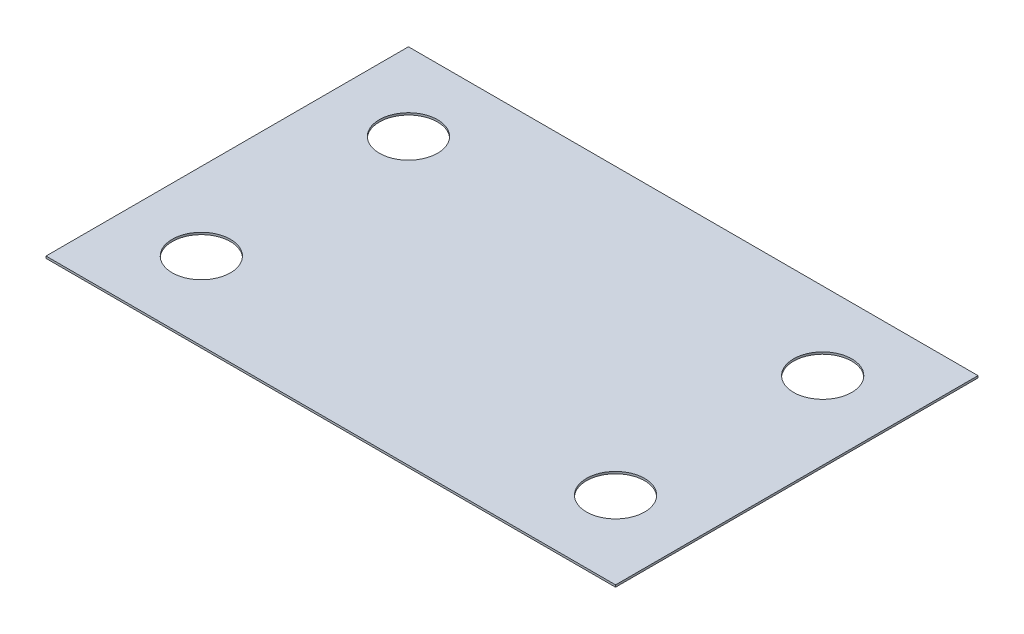
SolidWorks part; units mm, degrees
ref_plane "Front Plane" through (0, 0, 0) normal (0, 0, 1) x (1, 0, 0)
ref_plane "Top Plane" through (0, 0, 0) normal (0, 1, 0) x (1, 0, 0)
ref_plane "Right Plane" through (0, 0, 0) normal (1, 0, 0) x (0, 0, -1)
sketch "Sketch1" plane through (0, 0, 0) normal (0, 1, 0) x (1, 0, 0)
  line L0 (9.525, 9.525) -> (60.325, 9.525) construction
  line L1 (0, 0) -> (69.85, 0)
  line L2 (0, 0) -> (0, 44.45)
  line L3 (0, 44.45) -> (69.85, 44.45)
  line L4 (69.85, 0) -> (69.85, 44.45)
  line L5 (9.525, 9.525) -> (9.525, 34.925) construction
  circle A0 centre (34.925, 22.225) radius 1 construction
  circle A1 centre (9.525, 9.525) radius 3.5687
  circle A2 centre (9.525, 34.925) radius 3.5687
  circle A3 centre (60.325, 9.525) radius 3.5687
  circle A4 centre (60.325, 34.925) radius 3.5687
  point P8 (34.925, 44.45)
  point P10 (0, 22.225)
  point P17 (0, 0)
  point P18 (34.925, 9.525)
  point P19 (34.925, 0)
  point P20 (9.525, 22.225)
  dimension "D3" = 2
  dimension "D4" = 7.1374
  dimension "D1" = 44.45
  dimension "D2" = 69.85
  dimension "D5" = 50.8
  dimension "D6" = 25.4
extrude "Boss-Extrude1" add sketch "Sketch1" along normal blind 0.254
